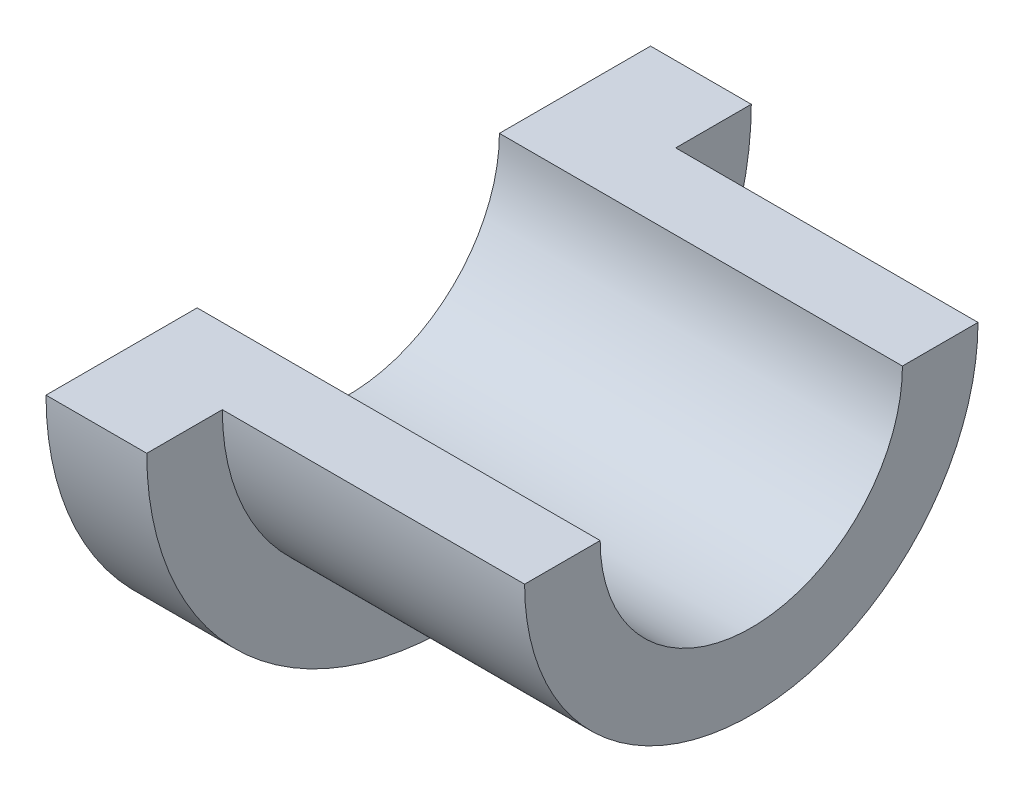
SolidWorks part; units mm, degrees
ref_plane "Front Plane" through (0, 0, 0) normal (0, 0, 1) x (1, 0, 0)
ref_plane "Top Plane" through (0, 0, 0) normal (0, 1, 0) x (1, 0, 0)
ref_plane "Right Plane" through (0, 0, 0) normal (1, 0, 0) x (0, 0, -1)
sketch "Sketch1" plane through (0, 0, 0) normal (1, 0, 0) x (0, 0, -1)
  circle A0 centre (-10.367, 4.3157) radius 6
  dimension "D1" = 12
extrude "Boss-Extrude1" add sketch "Sketch1" along normal blind 2
sketch "Sketch2" plane through (2, 0, 0) normal (1, 0, 0) x (0, 0, -1)
  circle A0 centre (-10.367, 4.3157) radius 4.5
  circle A1 centre (-10.367, 4.3157) radius 6 construction
  dimension "D1" = 9
extrude "Boss-Extrude2" add sketch "Sketch2" along normal blind 6
sketch "Sketch3" plane through (8, 0, 0) normal (1, 0, 0) x (0, 0, -1)
  circle A0 centre (-10.367, 4.3157) radius 3
  circle A1 centre (-10.367, 4.3157) radius 4.5 construction
  dimension "D1" = 6
extrude "Cut-Extrude1" cut sketch "Sketch3" against normal blind 11
sketch "Sketch4" plane through (8, 0, 0) normal (1, 0, 0) x (0, 0, -1)
  line L1 (-18.6737, 12.76) -> (-0.7753, 12.76)
  line L2 (-18.6737, 12.76) -> (-18.6737, 4.3157)
  line L3 (-18.6737, 4.3157) -> (-0.7753, 4.3157)
  line L4 (-0.7753, 12.76) -> (-0.7753, 4.3157)
  circle A0 centre (-10.367, 4.3157) radius 6 construction
  dimension "D1" = 0
extrude "Cut-Extrude2" cut sketch "Sketch4" against normal blind 11
